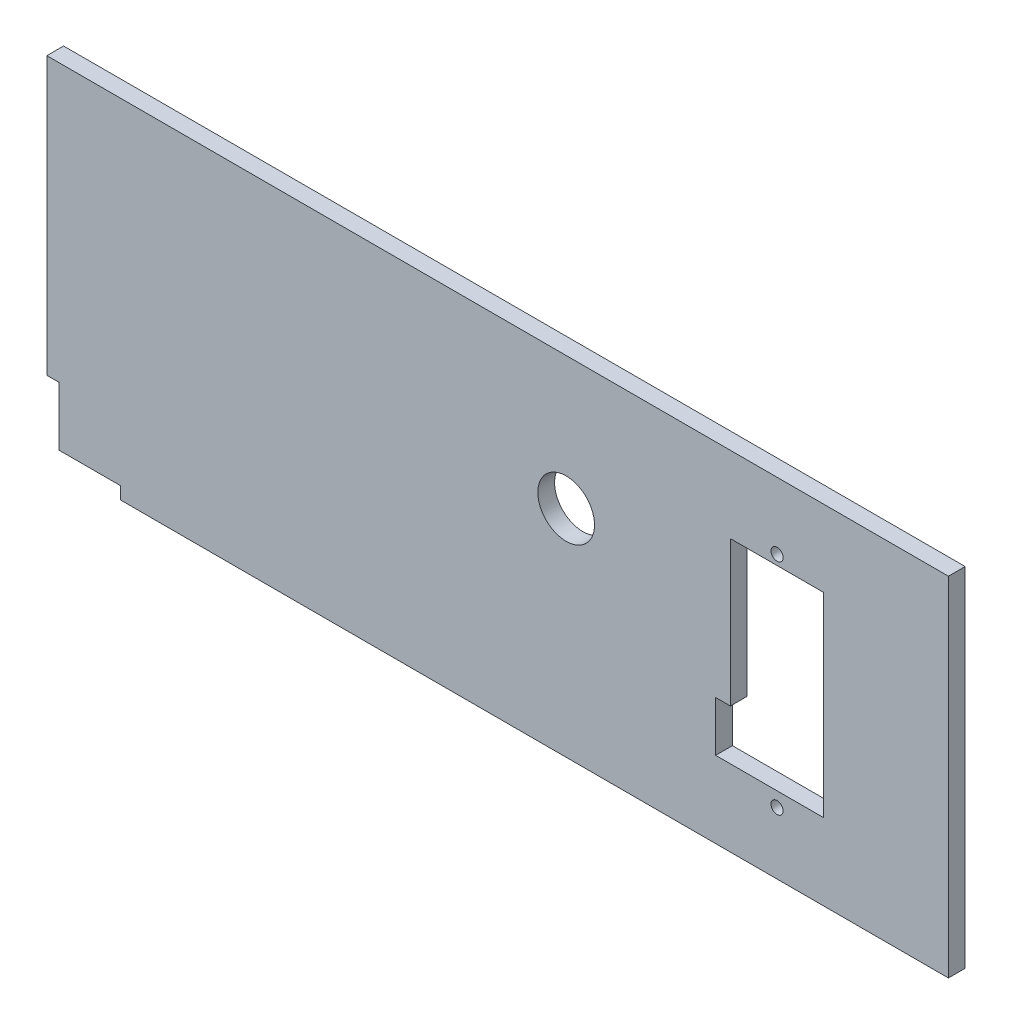
SolidWorks part; units mm, degrees
ref_plane "Front Plane" through (0, 0, 0) normal (0, 0, 1) x (1, 0, 0)
ref_plane "Top Plane" through (0, 0, 0) normal (0, 1, 0) x (1, 0, 0)
ref_plane "Right Plane" through (0, 0, 0) normal (1, 0, 0) x (0, 0, -1)
sketch "Sketch1" plane through (0, 0, 0) normal (0, 0, 1) x (1, 0, 0)
  line L3 (-1, 138) -> (341, 138)
  line L4 (341, 6) -> (341, 138)
  line L9 (293.7, 35) -> (252.7, 35)
  line L10 (293.7, 35) -> (293.7, 109)
  line L11 (293.7, 109) -> (258.3, 109)
  line L12 (258.3, 109) -> (258.3, 54)
  line L13 (258.3, 54) -> (252.7, 54)
  line L14 (252.7, 54) -> (252.7, 35)
  line L15 (341, 72) -> (-1, 72) construction
  line L16 (276, 109) -> (276, 112.7) construction
  line L17 (276, 29.5) -> (276, 109) construction
  line L18 (27, 10.7) -> (3.7, 10.7)
  line L19 (27, 10.7) -> (27, 6)
  line L20 (3.7, 10.7) -> (3.7, 33)
  line L21 (3.7, 33) -> (-1, 33)
  line L22 (-1, 138) -> (-1, 33)
  line L23 (27, 6) -> (341, 6)
  circle A0 centre (276, 112.7) radius 2.3
  circle A1 centre (276, 29.5) radius 2.3
  circle A2 centre (196, 87.7) radius 10.75
  point P0 (27, 8.35)
  point P4 (0, 0)
  point P13 (293.7, 72)
  point P14 (276, 109)
  dimension "D9" = 4.6
  dimension "D10" = 4.6
  dimension "D14" = 21.5
  dimension "D2" = 342
  dimension "D3" = 19
  dimension "D4" = 74
  dimension "D5" = 41
  dimension "D6" = 35.4
  dimension "D7" = 65
  dimension "D8" = 3.7
  dimension "D11" = 83.2
  dimension "D12" = 80
  dimension "D13" = 25
  dimension "D15" = 27
  dimension "D16" = 132
  dimension "D17" = 28
  dimension "D18" = 4.7
  dimension "D19" = 4.7
  dimension "D20" = 6
  dimension "D21" = 27
extrude "Boss-Extrude1" add sketch "Sketch1" along normal blind 6.35
